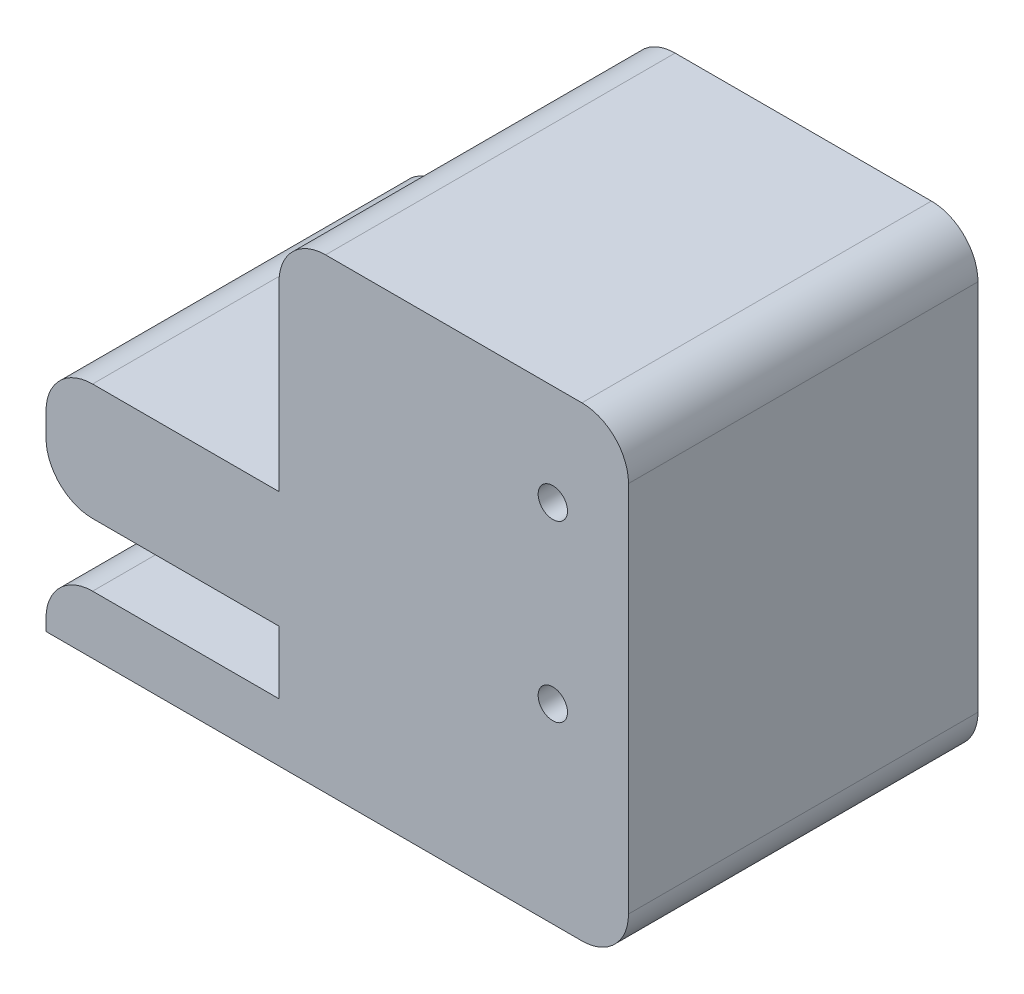
SolidWorks part; units mm, degrees
ref_plane "Front Plane" through (0, 0, 0) normal (0, 0, 1) x (1, 0, 0)
ref_plane "Top Plane" through (0, 0, 0) normal (0, 1, 0) x (1, 0, 0)
ref_plane "Right Plane" through (0, 0, 0) normal (1, 0, 0) x (0, 0, -1)
sketch "Sketch1" plane through (0, 0, 0) normal (0, 0, 1) x (1, 0, 0)
  line L0 (0, 0) -> (12.7, 0)
  line L1 (12.7, 0) -> (12.7, -3.429)
  line L2 (12.7, -3.429) -> (0, -3.429)
  line L3 (0, -3.429) -> (0, -6.604)
  line L4 (0, -6.604) -> (31.75, -6.604)
  line L5 (31.75, -6.604) -> (31.75, 18.796)
  line L6 (31.75, 18.796) -> (12.7, 18.796)
  line L7 (12.7, 18.796) -> (12.7, 6.35)
  line L8 (12.7, 6.35) -> (0, 6.35)
  line L9 (0, 6.35) -> (0, 0)
  dimension "D1" = 3.429
  dimension "D2" = 6.35
  dimension "D3" = 3.175
  dimension "D4" = 25.4
  dimension "D5" = 19.05
  dimension "D6" = 12.7
extrude "Boss-Extrude1" add sketch "Sketch1" along normal blind 19.05
hole_wizard "M4x0.7 Tapped Hole1" positions "Sketch2" profile "Sketch3" tap size "M4x0.7" standard "ANSI Metric" end condition up to next
sketch "Sketch2" plane through (0, 6.35, 0) normal (0, 1, 0) x (1, 0, 0)
  line L0 (6.35, 0) -> (6.35, -19.05) construction
  line L1 (12.7, 0) -> (0, 0) construction
  line L2 (12.7, -19.05) -> (0, -19.05) construction
  point P8 (6.35, -9.525)
sketch "Sketch3" plane through (6.35, 6.35, 9.525) normal (1, 0, 0) x (0, 0, 1)
  line L0 (0, 0) -> (0, 6.35)
  line L1 (0, 6.35) -> (1.65, 6.35)
  line L2 (1.65, 6.35) -> (1.65, 0)
  line L5 (1.65, 0) -> (0, 0)
  line L11 (0, -6.35) -> (0, 107.95) construction
  dimension "Thru Tap Drill Dia." = 3.3
  dimension "Thru Tap Drill Depth" = 6.35
cosmetic thread "Hole Thread1"
hole_wizard "M2x0.4 Tapped Hole1" positions "Sketch4" profile "Sketch5" tap size "M2x0.4" standard "ANSI Metric" end condition up to next
sketch "Sketch4" plane through (0, 0, 19.05) normal (0, 0, 1) x (1, 0, 0)
  point P0 (27.625, 13.296)
  point P3 (27.625, 3.796)
sketch "Sketch5" plane through (27.625, 13.296, 19.05) normal (1, 0, 0) x (0, -1, 0)
  line L0 (0, 0) -> (0, 19.05)
  line L1 (0, 19.05) -> (0.8, 19.05)
  line L2 (0.8, 19.05) -> (0.8, 0)
  line L5 (0.8, 0) -> (0, 0)
  line L11 (0, -6.35) -> (0, 107.95) construction
  dimension "Thru Tap Drill Dia." = 1.6
  dimension "Thru Tap Drill Depth" = 19.05
cosmetic thread "Hole Thread2"
cosmetic thread "Hole Thread3"
fillet "Fillet1" radius 2.54 6 edges at (0, 6.35, 9.525) (0, -3.429, 9.525) (0, 0, 9.525) (31.75, -6.604, 9.525) (31.75, 18.796, 9.525) (12.7, 18.796, 9.525)
